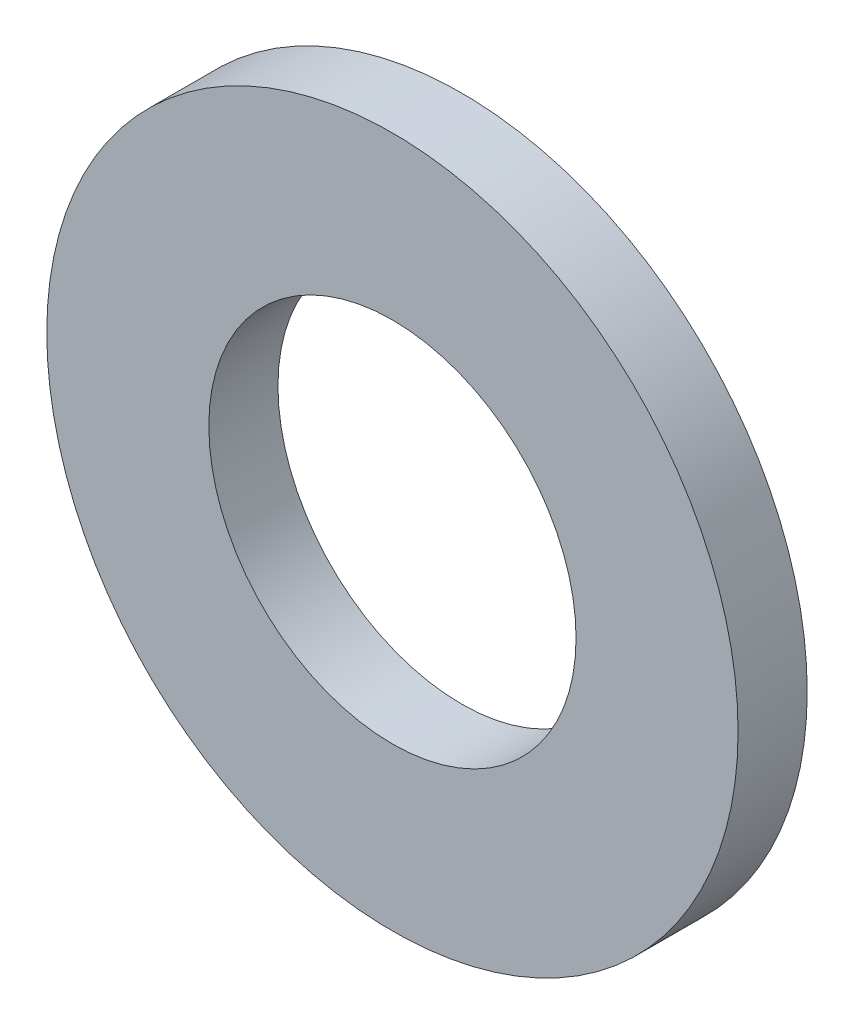
SolidWorks part; units mm, degrees
ref_plane "Front Plane" through (0, 0, 0) normal (0, 0, 1) x (1, 0, 0)
ref_plane "Top Plane" through (0, 0, 0) normal (0, 1, 0) x (1, 0, 0)
ref_plane "Right Plane" through (0, 0, 0) normal (1, 0, 0) x (0, 0, -1)
ref_plane "Plane1" through (0, 0, 0) normal (0, -1, 0) x (1, 0, 0)
sketch "Sketch1" plane through (0, 0, 0) normal (0, -1, 0) x (1, 0, 0)
  line L0 (8, 0) -> (8, 1.6)
  line L1 (8, 1.6) -> (4.25, 1.6)
  line L2 (4.25, 1.6) -> (4.25, 0)
  line L3 (4.25, 0) -> (8, 0)
  line L4 (0, 1.6) -> (0, 0) construction
revolve "Revolve1" add sketch "Sketch1" angle 360 about L4
